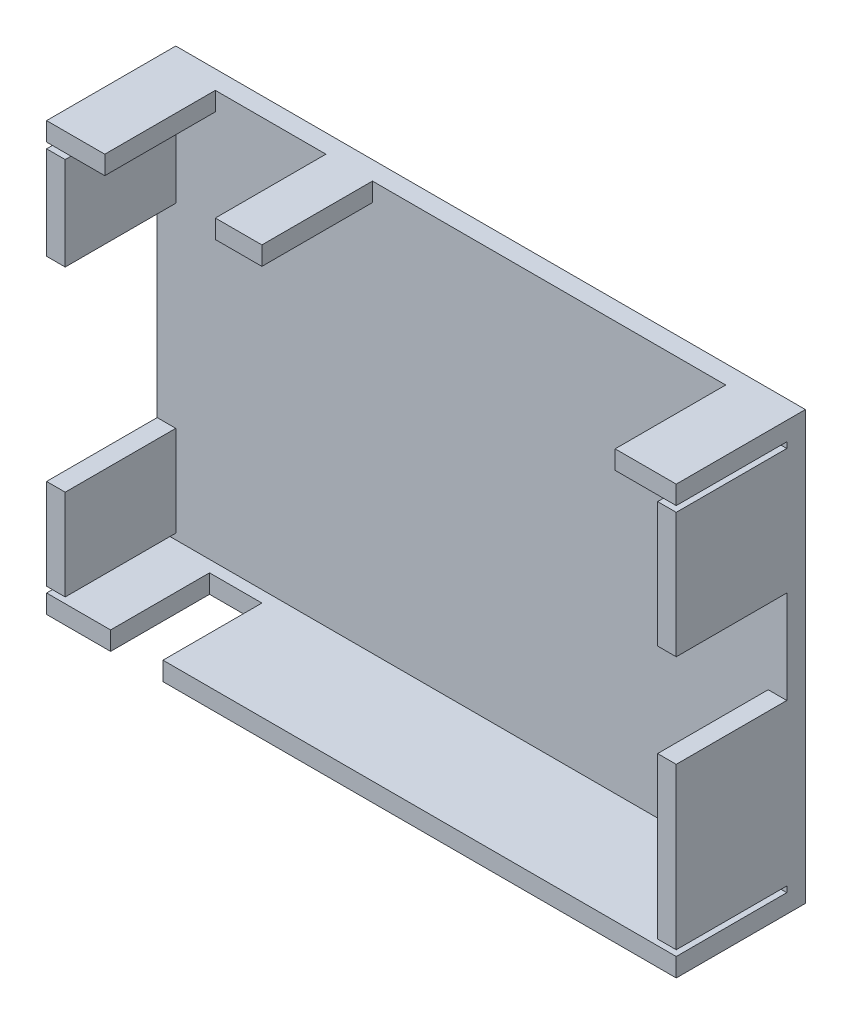
SolidWorks part; units mm, degrees
ref_plane "Front Plane" through (0, 0, 0) normal (0, 0, 1) x (1, 0, 0)
ref_plane "Top Plane" through (0, 0, 0) normal (0, 1, 0) x (1, 0, 0)
ref_plane "Right Plane" through (0, 0, 0) normal (1, 0, 0) x (0, 0, -1)
sketch "Sketch1" plane through (0, 0, 0) normal (0, 0, 1) x (1, 0, 0)
  line L1 (0, 0) -> (108.2, 0)
  line L2 (0, 0) -> (0, 73.5)
  line L3 (0, 73.5) -> (108.2, 73.5)
  line L4 (108.2, 0) -> (108.2, 73.5)
  dimension "D1" = 73.5
  dimension "D2" = 108.2
extrude "Boss-Extrude2" add sketch "Sketch1" along normal blind 3.2
sketch "Sketch2" plane through (0, 0, 3.2) normal (0, 0, 1) x (1, 0, 0)
  line L1 (3.2, 3.2) -> (105, 3.2)
  line L2 (3.2, 3.2) -> (3.2, 70.3)
  line L3 (3.2, 70.3) -> (105, 70.3)
  line L4 (0, 73.5) -> (0, 0)
  line L5 (0, 0) -> (108.2, 0)
  line L6 (108.2, 0) -> (108.2, 73.5)
  line L7 (108.2, 73.5) -> (0, 73.5)
  line L8 (0, 73.5) -> (0, 0)
  line L9 (0, 0) -> (108.2, 0)
  line L10 (108.2, 0) -> (108.2, 73.5)
  line L11 (108.2, 73.5) -> (0, 73.5)
  line L12 (105, 3.2) -> (105, 70.3)
  dimension "D2" = 3.2
  dimension "D3" = 3.2
  dimension "D4" = 3.2
  dimension "D5" = 3.2
  dimension "D1" = 0
extrude "Boss-Extrude3" add sketch "Sketch2" along normal blind 19
sketch "Sketch3" plane through (0, 0, 22.2) normal (0, 0, 1) x (1, 0, 0)
  line L0 (3.2, 70.3) -> (0, 70.3)
  line L1 (0, 70.3) -> (0, 69.3)
  line L2 (0, 69.3) -> (3.2, 69.3)
  line L3 (3.2, 70.3) -> (3.2, 3.2) construction
  line L4 (108.2, 73.5) -> (0, 73.5)
  line L5 (0, 73.5) -> (0, 0)
  line L6 (0, 0) -> (108.2, 0)
  line L7 (108.2, 0) -> (108.2, 73.5)
  line L9 (0, 70.3) -> (0, 69.3)
  line L11 (108.2, 3.2) -> (108.2, 4.2)
  line L12 (3.2, 69.3) -> (3.2, 70.3)
  line L13 (105, 70.3) -> (108.2, 70.3)
  line L14 (108.2, 70.3) -> (108.2, 69.3)
  line L15 (108.2, 69.3) -> (105, 69.3)
  line L16 (105, 3.2) -> (105, 70.3) construction
  line L17 (105, 69.3) -> (105, 70.3)
  line L18 (105, 3.2) -> (108.2, 3.2)
  line L19 (108.2, 3.2) -> (108.2, 4.2)
  line L20 (108.2, 4.2) -> (105, 4.2)
  line L21 (105, 4.2) -> (105, 3.2)
  line L22 (3.2, 3.2) -> (0, 3.2)
  line L23 (0, 3.2) -> (0, 4.2)
  line L24 (0, 4.2) -> (3.2, 4.2)
  line L25 (3.2, 4.2) -> (3.2, 3.2)
  line L26 (0, 4.2) -> (0, 0)
  line L27 (108.2, 69.3) -> (108.2, 70.3)
  line M10 (0, 73.5) -> (0, 0)
  line M12 (108.2, 0) -> (108.2, 73.5)
  line M14 (3.2, 3.2) -> (3.2, 70.3)
  line M16 (105, 70.3) -> (105, 3.2)
  dimension "D1" = 0
  dimension "D2" = 1
  dimension "D3" = 1
  dimension "D4" = 1
  dimension "D5" = 1
extrude "Cut-Extrude1" cut sketch "Sketch3" against normal blind 19 contours L2 L0 M10 M14 | L15 L13 M12 M16 | L20 L18 M12 M16 | L24 L25 L22 L23
sketch "Sketch4" plane through (0, 0, 22.2) normal (0, 0, 1) x (1, 0, 0)
  line L0 (0, 53.3) -> (3.2, 53.3)
  line L1 (0, 19.8) -> (3.2, 19.8)
  line L4 (0, 69.3) -> (0, 4.2)
  line L5 (0, 4.2) -> (3.2, 4.2)
  line L6 (3.2, 4.2) -> (3.2, 69.3)
  line L7 (3.2, 69.3) -> (0, 69.3)
  line L8 (0, 53.3) -> (0, 19.8)
  line L9 (0, 4.2) -> (3.2, 4.2) construction
  line L10 (3.2, 19.8) -> (3.2, 53.3)
  line L11 (3.2, 69.3) -> (0, 69.3) construction
  dimension "D2" = 16
  dimension "D3" = 33.5
  dimension "D1" = 0
extrude "Cut-Extrude2" cut sketch "Sketch4" against normal blind 19
sketch "Sketch5" plane through (0, 0, 22.2) normal (0, 0, 1) x (1, 0, 0)
  line L0 (10, 73.5) -> (10, 70.3)
  line L1 (29, 73.5) -> (29, 70.3)
  line L2 (37, 73.5) -> (37, 70.3)
  line L3 (97.7, 73.5) -> (97.7, 70.3)
  line L4 (0, 70.3) -> (108.2, 70.3)
  line L5 (108.2, 70.3) -> (108.2, 73.5)
  line L6 (108.2, 73.5) -> (0, 73.5)
  line L7 (0, 73.5) -> (0, 70.3)
  line L8 (10, 70.3) -> (29, 70.3)
  line L9 (108.2, 70.3) -> (108.2, 73.5) construction
  line L10 (97.7, 73.5) -> (37, 73.5)
  line L11 (0, 73.5) -> (0, 70.3) construction
  line L12 (29, 73.5) -> (10, 73.5)
  line L13 (37, 70.3) -> (97.7, 70.3)
  dimension "D2" = 10
  dimension "D3" = 19
  dimension "D4" = 8
  dimension "D5" = 10.5
  dimension "D1" = 0
extrude "Cut-Extrude3" cut sketch "Sketch5" against normal blind 19
sketch "Sketch6" plane through (0, 0, 22.2) normal (0, 0, 1) x (1, 0, 0)
  line L0 (105, 31.8) -> (108.2, 31.8)
  line L1 (105, 47.8) -> (108.2, 47.8)
  line L4 (105, 4.2) -> (108.2, 4.2)
  line L5 (108.2, 4.2) -> (108.2, 69.3)
  line L6 (108.2, 69.3) -> (105, 69.3)
  line L7 (105, 69.3) -> (105, 4.2)
  line L8 (105, 4.2) -> (108.2, 4.2) construction
  line L9 (108.2, 31.8) -> (108.2, 47.8)
  line L10 (108.2, 69.3) -> (105, 69.3) construction
  line L11 (105, 47.8) -> (105, 31.8)
  dimension "D2" = 21.5
  dimension "D3" = 16
  dimension "D1" = 0
extrude "Cut-Extrude4" cut sketch "Sketch6" against normal blind 19
sketch "Sketch7" plane through (0, 0, 22.2) normal (0, 0, 1) x (1, 0, 0)
  line L0 (11, 3.2) -> (11, 0)
  line L1 (20, 3.2) -> (20, 0)
  line L4 (108.2, 3.2) -> (0, 3.2)
  line L5 (0, 3.2) -> (0, 0)
  line L6 (0, 0) -> (108.2, 0)
  line L7 (108.2, 0) -> (108.2, 3.2)
  line L8 (20, 3.2) -> (11, 3.2)
  line L9 (0, 3.2) -> (0, 0) construction
  line L10 (11, 0) -> (20, 0)
  line L11 (108.2, 0) -> (108.2, 3.2) construction
  dimension "D2" = 11
  dimension "D3" = 9
  dimension "D1" = 0
extrude "Cut-Extrude5" cut sketch "Sketch7" against normal blind 17
equation "\"WallThickness\"= 3.2mm"
equation "\"D2@Sketch2\"=\"WallThickness\""
equation "\"D3@Sketch2\"=\"WallThickness\""
equation "\"D4@Sketch2\"=\"WallThickness\""
equation "\"D5@Sketch2\"=\"WallThickness\""
equation "\"CornerBreakDist\"= 1mm"
equation "\"D2@Sketch3\"=\"CornerBreakDist\""
equation "\"D3@Sketch3\"=\"CornerBreakDist\""
equation "\"D4@Sketch3\"=\"CornerBreakDist\""
equation "\"D5@Sketch3\"=\"CornerBreakDist\""
